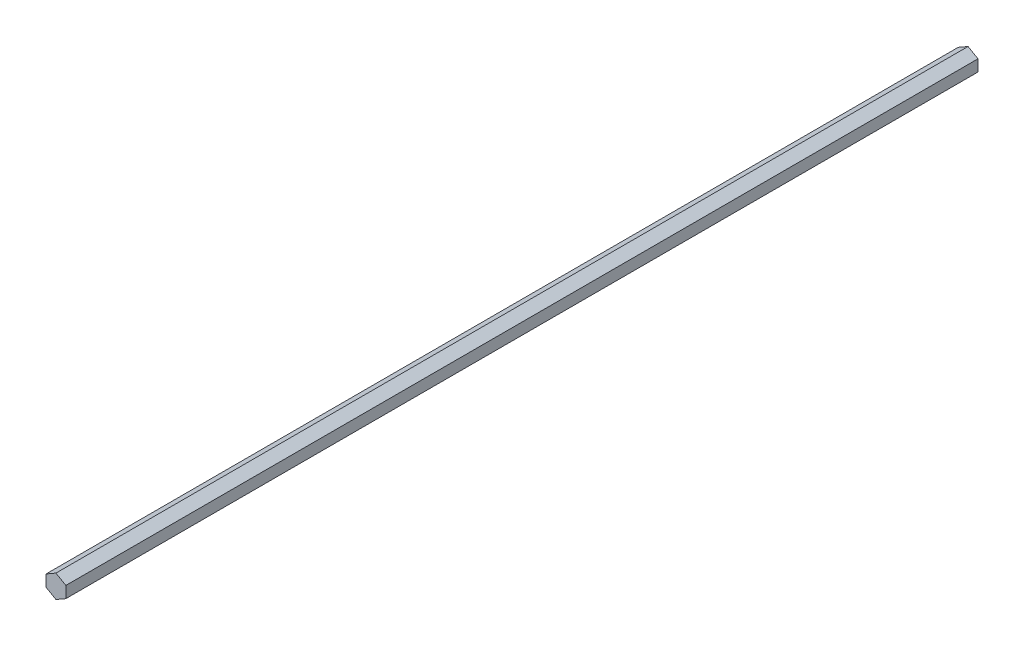
SolidWorks part; units mm, degrees
ref_plane "Front Plane" through (0, 0, 0) normal (0, 0, 1) x (1, 0, 0)
ref_plane "Top Plane" through (0, 0, 0) normal (0, 1, 0) x (1, 0, 0)
ref_plane "Right Plane" through (0, 0, 0) normal (1, 0, 0) x (0, 0, -1)
sketch "Sketch1" plane through (0, 0, 0) normal (0, 0, 1) x (1, 0, 0)
  line L1 (0, 7.3323) -> (-6.35, 3.6662)
  line L2 (-6.35, 3.6662) -> (-6.35, -3.6662)
  line L3 (-6.35, -3.6662) -> (0, -7.3323)
  line L4 (0, -7.3323) -> (6.35, -3.6662)
  line L5 (6.35, -3.6662) -> (6.35, 3.6662)
  line L6 (6.35, 3.6662) -> (0, 7.3323)
  circle A0 centre (0, 0) radius 6.35 construction
  point P1 (0, 0)
  dimension "D1" = 12.7
extrude "Boss-Extrude1" add sketch "Sketch1" along normal mid plane 584.2
